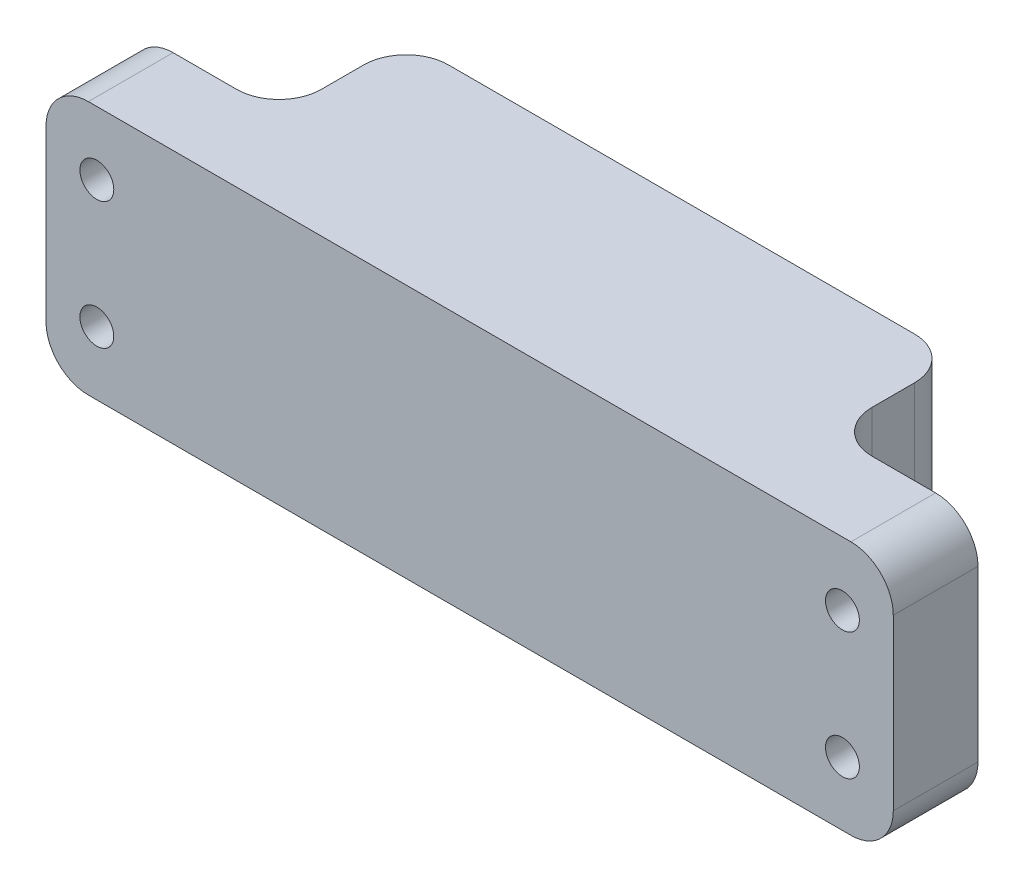
SolidWorks part; units mm, degrees
ref_plane "Front Plane" through (0, 0, 0) normal (0, 0, 1) x (1, 0, 0)
ref_plane "Top Plane" through (0, 0, 0) normal (0, 1, 0) x (1, 0, 0)
ref_plane "Right Plane" through (0, 0, 0) normal (1, 0, 0) x (0, 0, -1)
sketch "Sketch1" plane through (0, 0, 0) normal (0, 1, 0) x (1, 0, 0)
  line L0 (-100, -5) -> (-65, -5)
  line L1 (-100, -25) -> (100, -25)
  line L2 (-100, -25) -> (-100, 25)
  line L3 (-100, 25) -> (100, 25)
  line L4 (100, -25) -> (100, 25)
  line L5 (-100, -25) -> (100, 25) construction
  line L6 (-100, 25) -> (100, -25) construction
  line L7 (-65, -5) -> (-65, 25)
  line L8 (-65, 25) -> (65, 25)
  line L9 (65, 25) -> (65, -5)
  line L10 (65, -5) -> (100, -5)
  line L11 (0, 0) -> (0, -11.4821) construction
  point P0 (0, 0)
  dimension "D1" = 50
  dimension "D2" = 20
  dimension "D3" = 35
  dimension "D4" = 200
extrude "Boss-Extrude1" add sketch "Sketch1" along normal blind 60 contours L10 L9 L3 L7 L0 L2 L1 L4
fillet "Fillet1" radius 10 8 edges at (-65, 30, -25) (-100, 0, 15) (-65, 30, 5) (-100, 60, 15) (100, 0, 15) (100, 60, 15) (65, 30, -25) (65, 30, 5)
sketch "Sketch2" plane through (0, 0, 5) normal (0, 0, -1) x (-1, 0, 0)
  line L0 (0, 0) -> (0, 76.4227) construction
  line L1 (-100, 30) -> (-45.6065, 30) construction
  line L2 (-100, 50) -> (-100, 10) construction
  circle A1 centre (-88, 45) radius 4
  circle A2 centre (-88, 15) radius 4
  circle A3 centre (88, 15) radius 4
  circle A4 centre (88, 45) radius 4
  dimension "D1" = 8
  dimension "D2" = 30
  dimension "D3" = 12
extrude "Cut-Extrude1" cut sketch "Sketch2" against normal through all
sketch "Sketch3" plane through (0, 0, 5) normal (0, 0, -1) x (-1, 0, 0)
  circle A0 centre (88, 15) radius 4 construction
  circle A1 centre (88, 45) radius 4 construction
  circle A2 centre (-88, 15) radius 4 construction
  circle A3 centre (-88, 45) radius 4 construction
  circle A4 centre (88, 15) radius 4
  circle A5 centre (88, 45) radius 4
  circle A6 centre (-88, 15) radius 4
  circle A7 centre (-88, 45) radius 4
  circle A8 centre (88, 15) radius 6
  circle A9 centre (88, 45) radius 6
  circle A10 centre (-88, 15) radius 6
  circle A11 centre (-88, 45) radius 6
  dimension "D1" = 2
extrude "Cut-Extrude2" cut sketch "Sketch3" against normal blind 10
